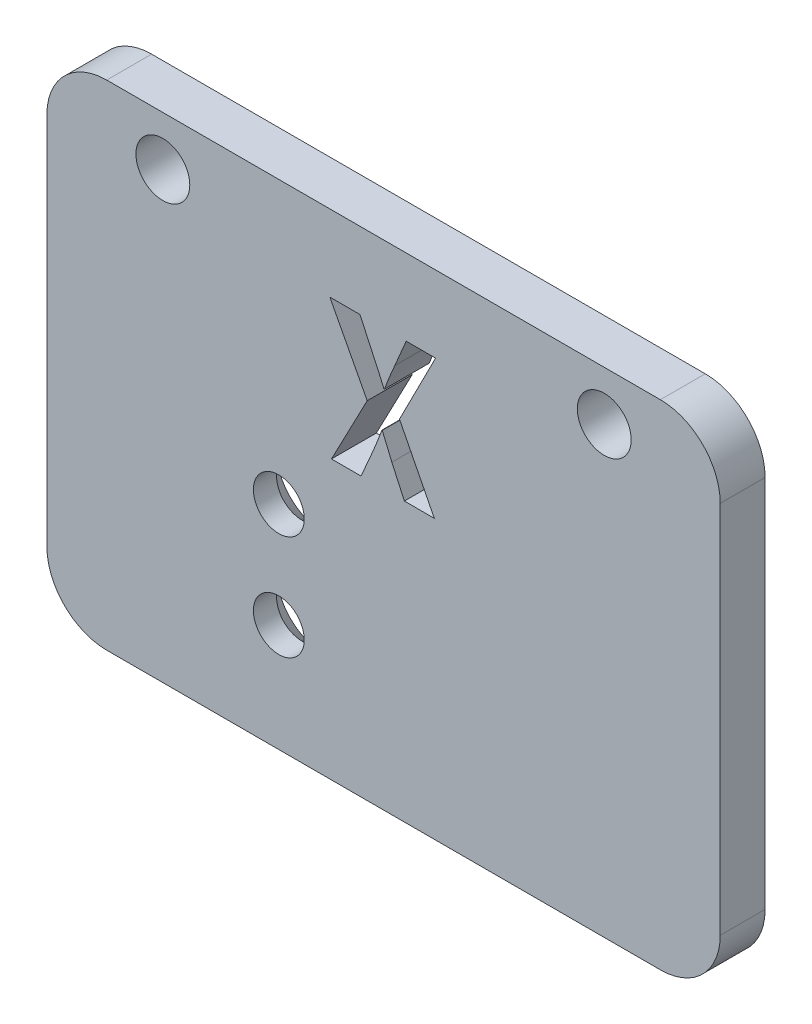
SolidWorks part; units mm, degrees
ref_plane "Front Plane" through (0, 0, 0) normal (0, 0, 1) x (1, 0, 0)
ref_plane "Top Plane" through (0, 0, 0) normal (0, 1, 0) x (1, 0, 0)
ref_plane "Right Plane" through (0, 0, 0) normal (1, 0, 0) x (0, 0, -1)
sketch "Sketch1" plane through (0, 0, 0) normal (0, 0, 1) x (1, 0, 0)
  line L0 (22.5, -9.7) -> (-22.5, -9.7) construction
  line L1 (22.5, 19.3) -> (-22.5, 19.3)
  line L2 (14.75, 16) -> (-14.75, 16) construction
  line L3 (20, -22) -> (30, -22) construction
  line L4 (12.2, 3.7) -> (-8.5, 3.7)
  line L5 (-10.5, 1.7) -> (-10.5, -7.7)
  line L6 (-8.5, -9.7) -> (12.2, -9.7)
  line L7 (12.2, -9.7) -> (12.2, 3.7)
  line L8 (12.2, 3.7) -> (-8.5, 3.7) construction
  line L9 (-10.5, 1.7) -> (-10.5, -7.7) construction
  line L10 (-8.5, -9.7) -> (12.2, -9.7) construction
  line L11 (12.2, -9.7) -> (12.2, 3.7) construction
  line L12 (0, 16) -> (0, 19.3) construction
  line L13 (0, 16) -> (0, 0) construction
  line L14 (0, 0) -> (0, -9.7) construction
  line L15 (22.5, -9.7) -> (22.5, 19.3)
  line L16 (-22.5, -9.7) -> (-22.5, 19.3)
  line L17 (22.5, 14.2) -> (-22.5, 14.2) construction
  line L18 (-22.5, -13.7) -> (22.5, -13.7)
  line L19 (-22.5, -13.7) -> (-22.5, -9.7)
  line L20 (22.5, -13.7) -> (22.5, -9.7)
  arc A0 (-7, 2.25) -> (-7, -1.25) centre (-7, 0.5) ccw construction
  arc A1 (-7, -1.25) -> (-7, 2.25) centre (-7, 0.5) ccw construction
  arc A2 (-8.5, 3.7) -> (-10.5, 1.7) centre (-8.5, 1.7) ccw
  arc A3 (-10.5, -7.7) -> (-8.5, -9.7) centre (-8.5, -7.7) ccw
  arc A4 (-8.5, 3.7) -> (-10.5, 1.7) centre (-8.5, 1.7) ccw construction
  arc A5 (-10.5, -7.7) -> (-8.5, -9.7) centre (-8.5, -7.7) ccw construction
  arc A6 (-7, -4.75) -> (-7, -8.25) centre (-7, -6.5) ccw construction
  arc A7 (-7, -8.25) -> (-7, -4.75) centre (-7, -6.5) ccw construction
  arc A8 (-7, 2.25) -> (-7, -1.25) centre (-7, 0.5) ccw construction
  arc A9 (-7, -1.25) -> (-7, 2.25) centre (-7, 0.5) ccw construction
  arc A10 (-7, -4.75) -> (-7, -8.25) centre (-7, -6.5) ccw construction
  arc A11 (-7, -8.25) -> (-7, -4.75) centre (-7, -6.5) ccw construction
  circle A12 centre (14.75, 16) radius 1.8
  circle A13 centre (-14.75, 16) radius 1.8
  text T0 "X" font "@Adobe Gothic Std B" height in points 30
  point P19 (1.85, -9.7)
  point P22 (0, 19.3)
  point P32 (0, -9.7)
  point P40 (0, -13.7)
  dimension "D6" = 3.6
  dimension "D7" = 3.6
  dimension "D2" = 29
  dimension "D3" = 38
  dimension "D4" = 45
  dimension "D5" = 29.5
  dimension "D8" = 4
  dimension "D1" = 0
extrude "Boss-Extrude1" add sketch "Sketch1" along normal blind 3
fillet "Fillet1" radius 4 4 edges at (-22.5, 19.3, 1.5) (22.5, 19.3, 1.5) (22.5, -13.7, 1.5) (-22.5, -13.7, 1.5)
sketch "Sketch3" plane through (0, 0, 0) normal (0, 0, -1) x (-1, 0, 0)
  point P0 (7, -6.5)
  point P1 (7, 0.5)
  point P3 (7, -6.5)
hole_wizard "CSK for M3 Countersunk Flat Head Screw1" positions "3DSketch4" profile "Sketch6" countersink size "M3" standard "DIN" end condition through all
sketch3d "3DSketch4"
  point P0 (-7, -6.5, 0)
  point P3 (-7, 0.5, 0)
sketch "Sketch6" plane through (-7, -6.5, 0) normal (1, 0, 0) x (0, 1, 0)
  line L0 (0, 0) -> (0, 3)
  line L1 (0, 3) -> (1.7, 3)
  line L2 (1.7, 3) -> (1.7, 1.45)
  line L3 (1.7, 1.45) -> (3.15, 0)
  line L5 (3.15, 0) -> (0, 0)
  line L6 (-1.7, 1.45) -> (-3.15, 0) construction
  line L11 (0, -6.35) -> (0, 107.95) construction
  dimension "Thru Hole Dia." = 3.4
  dimension "Thru Hole Depth" = 3
  dimension "Near C'Sink Dia." = 6.3
  dimension "Near C'Sink Angle" = 90
